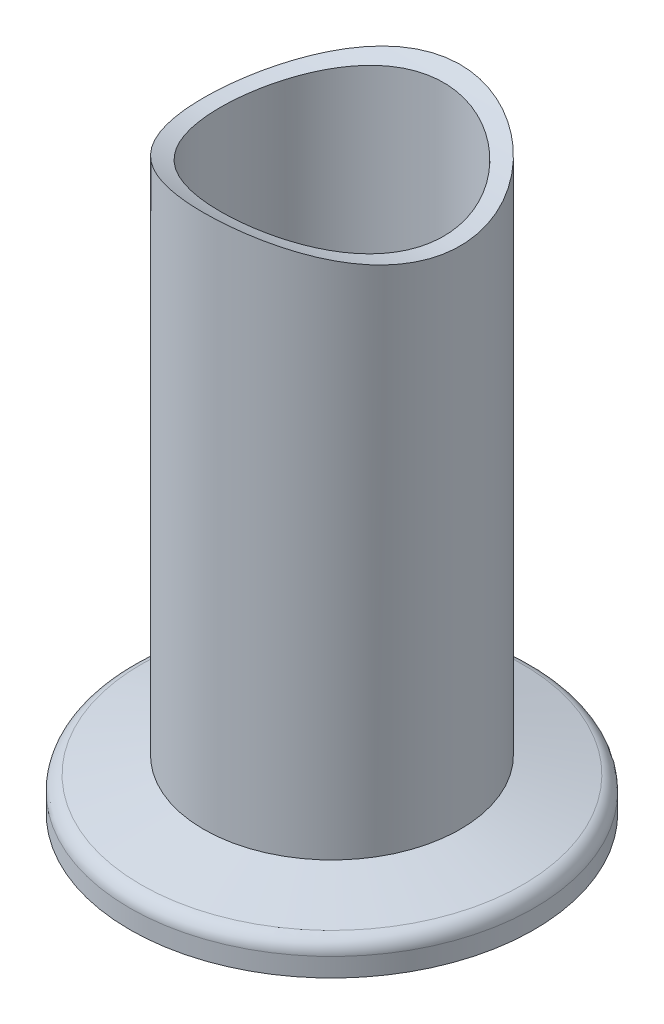
SolidWorks part; units mm, degrees
ref_plane "Front Plane" through (0, 0, 0) normal (0, 0, 1) x (1, 0, 0)
ref_plane "Top Plane" through (0, 0, 0) normal (0, 1, 0) x (1, 0, 0)
ref_plane "Right Plane" through (0, 0, 0) normal (1, 0, 0) x (0, 0, -1)
ref_plane "Plane1" through (0, 0, 0) normal (0, 0, -1) x (-1, 0, 0)
sketch "Sketch1" plane through (0, 0, 0) normal (0, 0, -1) x (-1, 0, 0)
  line L0 (-12.7, 4.956) -> (-18.8882, 3.2979)
  line L1 (-20, 1.849) -> (-20, 0)
  line L2 (-20, 0) -> (-11.85, 0)
  line L3 (-11.85, 0) -> (-11.85, 2.5)
  line L4 (-11.85, 2.5) -> (-11.05, 2.5)
  line L5 (-11.05, 2.5) -> (-11.05, 70)
  line L6 (-11.05, 70) -> (-12.7, 70)
  line L7 (-12.7, 70) -> (-12.7, 4.956)
  line L8 (0, 0) -> (0, 70) construction
  arc A0 (-18.8882, 3.2979) -> (-20, 1.849) centre (-18.5, 1.849) ccw
revolve "Revolve1" add sketch "Sketch1" angle 360 about L8
sketch "Sketch2" plane through (0, 0, 0) normal (1, 0, 0) x (0, 0, -1)
  line L1 (-12.7, 4.956) -> (12.7, 4.956) construction
  circle A0 centre (0, 84.706) radius 29.75
  point P8 (0, 54.956)
  dimension "D1" = 59.5
  dimension "D2" = 50
extrude "Cut-Extrude2" cut sketch "Sketch2" against normal through all both and the other way through all
